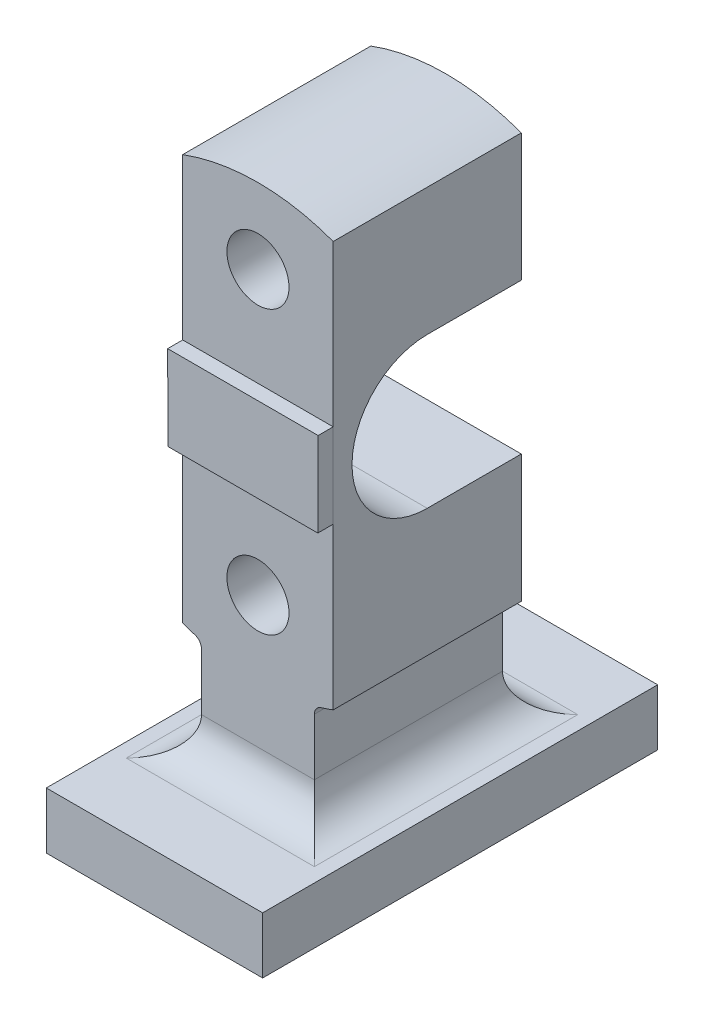
SolidWorks part; units mm, degrees
ref_plane "Front Plane" through (0, 0, 0) normal (0, 0, 1) x (1, 0, 0)
ref_plane "Top Plane" through (0, 0, 0) normal (0, 1, 0) x (1, 0, 0)
ref_plane "Right Plane" through (0, 0, 0) normal (1, 0, 0) x (0, 0, -1)
sketch "Sketch1" plane through (0, 0, 0) normal (0, 0, 1) x (1, 0, 0)
  line L0 (40, 0) -> (-40, 0)
  line L1 (40, 107.8193) -> (40, -107.8193)
  line L2 (-40, 107.8193) -> (-40, -107.8193)
  line L3 (0, 75) -> (0, -75) construction
  line L4 (0, 36.1528) -> (0, -91.5) construction
  line L5 (-30, -165) -> (30, -165)
  line L6 (-30, -111.018) -> (-30, -165)
  line L7 (30, -111.018) -> (30, -165)
  arc A0 (-40, -107.8193) -> (-30, -111.018) centre (0, 0) ccw
  circle A1 centre (0, 75) radius 16.5
  circle A2 centre (0, -75) radius 16.5
  arc A3 (40, 107.8193) -> (-40, 107.8193) centre (0, 0) ccw
  arc A4 (30, -111.018) -> (40, -107.8193) centre (0, 0) ccw
  point P5 (0, 0)
  point P9 (40, 0)
  point P12 (-40, 0)
  point P18 (0, -91.5)
  dimension "D3" = 33
extrude "Boss-Extrude1" add sketch "Sketch1" against normal mid plane 100 contours L7 A4 L1 L0 L2 A0 L6 L5 A2 | L1 A3 L2 L0 A1
sketch "Sketch4" plane through (0, 0, 0) normal (0, 0, 1) x (1, 0, 0)
  line L0 (57.5, -165) -> (-57.5, -165)
  line L2 (-57.5, -165) -> (-57.5, -195)
  line L3 (-57.5, -195) -> (57.5, -195)
  line L4 (57.5, -195) -> (57.5, -165)
  point P3 (0, -165)
extrude "Boss-Extrude2" add sketch "Sketch4" along normal mid plane 210
fillet "Fillet1" radius 20 1 edges at (-30, -165, 0)
fillet "Fillet2" radius 20 1 edges at (-10, -165, 50)
fillet "Fillet3" radius 20 1 edges at (-10, -165, -50)
fillet "Fillet4" radius 20 1 edges at (30, -165, 0)
fillet "Fillet5" radius 5 2 edges at (30, -111.018, 0) (-30, -111.018, 0)
sketch "Sketch6" plane through (-40, 0, 0) normal (-1, 0, 0) x (0, 0, 1)
  line L0 (0, 40) -> (-50, 40)
  line L1 (-50, 107.8193) -> (-50, -107.8193) construction
  line L2 (0, -40) -> (-50, -40)
  line L7 (50, -107.8193) -> (50, 107.8193)
  line L8 (50, 107.8193) -> (-50, 107.8193)
  line L9 (-50, 107.8193) -> (-50, -107.8193)
  line L10 (-50, -107.8193) -> (50, -107.8193)
  line L13 (-50, 40) -> (-50, -40)
  arc A0 (0, -40) -> (0, 40) centre (0, 0) ccw
  dimension "D1" = 80
  dimension "D2" = 0
extrude "Cut-Extrude2" cut sketch "Sketch6" against normal blind 138
sketch "Sketch8" plane through (0, 0, 50) normal (0, 0, 1) x (1, 0, 0)
  line L2 (-39.8174, -22.5) -> (-40, 22.5)
  line L3 (-40, 107.8193) -> (-40, -107.8193) construction
  line L4 (-39.8174, -20.93) -> (-40, 22.5)
  line L5 (-40, 22.5) -> (40, 22.5)
  line L6 (39.8174, -22.5) -> (40, 22.5)
  line L7 (-39.8174, -22.5) -> (39.8174, -22.5)
  point P6 (0, 0)
  point P12 (-39.9087, 0)
  point P14 (-39.9087, 1.57)
extrude "Boss-Extrude4" add sketch "Sketch8" along normal blind 8
